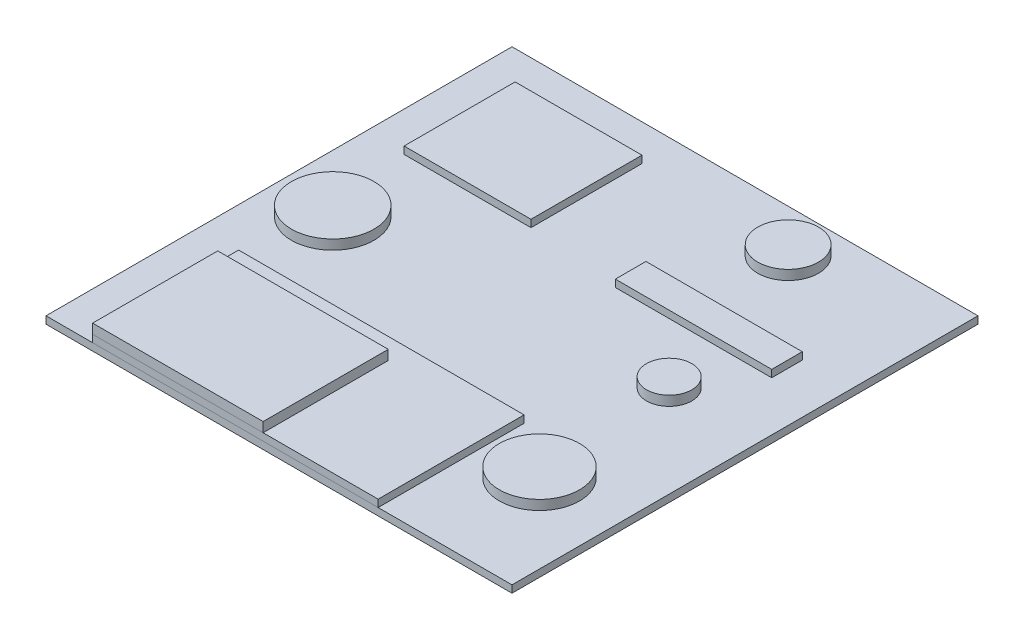
SolidWorks part; units mm, degrees
ref_plane "Front Plane" through (0, 0, 0) normal (0, 0, 1) x (1, 0, 0)
ref_plane "Top Plane" through (0, 0, 0) normal (0, 1, 0) x (1, 0, 0)
ref_plane "Right Plane" through (0, 0, 0) normal (1, 0, 0) x (0, 0, -1)
sketch "Sketch1" plane through (0, 0, 0) normal (0, 1, 0) x (1, 0, 0)
  line L1 (-609.6, -609.6) -> (609.6, -609.6)
  line L2 (-609.6, -609.6) -> (-609.6, 609.6)
  line L3 (-609.6, 609.6) -> (609.6, 609.6)
  line L4 (609.6, -609.6) -> (609.6, 609.6)
  line L5 (-609.6, -609.6) -> (609.6, 609.6) construction
  line L6 (-609.6, 609.6) -> (609.6, -609.6) construction
  point P0 (0, 0)
  dimension "D1" = 1219.2
  dimension "D2" = 1219.2
extrude "Extrude1" add sketch "Sketch1" along normal blind 19.05
sketch "Sketch2" plane through (0, 19.05, 0) normal (0, 1, 0) x (1, 0, 0)
  line L0 (-609.6, -609.6) -> (609.6, -609.6) construction
  line L1 (-506.8128, 514.9633) -> (-174.8652, 514.9633)
  line L2 (-506.8128, 514.9633) -> (-506.8128, 224.5092)
  line L3 (-506.8128, 224.5092) -> (-174.8652, 224.5092)
  line L4 (-174.8652, 514.9633) -> (-174.8652, 224.5092)
  line L5 (-506.8128, 514.9633) -> (-174.8652, 224.5092) construction
  line L6 (-506.8128, 224.5092) -> (-174.8652, 514.9633) construction
  line L7 (71.1316, 279.3398) -> (480.1384, 279.3398)
  line L8 (71.1316, 279.3398) -> (71.1316, 199.3167)
  line L9 (71.1316, 199.3167) -> (480.1384, 199.3167)
  line L10 (480.1384, 279.3398) -> (480.1384, 199.3167)
  line L11 (71.1316, 279.3398) -> (480.1384, 199.3167) construction
  line L12 (71.1316, 199.3167) -> (480.1384, 279.3398) construction
  line L13 (-487.548, -227.6784) -> (259.334, -227.6784)
  line L14 (-487.548, -227.6784) -> (-487.548, -609.6)
  line L15 (-487.548, -609.6) -> (259.334, -609.6)
  line L16 (259.334, -227.6784) -> (259.334, -609.6)
  line L17 (-487.548, -227.6784) -> (259.334, -609.6) construction
  line L18 (-487.548, -609.6) -> (259.334, -227.6784) construction
  point P0 (-340.839, 369.7362)
  point P5 (275.635, 239.3283)
  point P10 (-114.107, -418.6392)
extrude "Extrude2" add sketch "Sketch2" along normal blind 19.05 separate body
sketch "Sketch3" plane through (0, 38.1, 0) normal (0, 1, 0) x (1, 0, 0)
  line L0 (-487.548, -227.6784) -> (-487.548, -609.6) construction
  line L1 (-487.548, -282.3036) -> (-41.4934, -282.3036)
  line L2 (-487.548, -282.3036) -> (-487.548, -609.6)
  line L3 (-487.548, -609.6) -> (-41.4934, -609.6)
  line L4 (-41.4934, -282.3036) -> (-41.4934, -609.6)
  line L5 (-487.548, -609.6) -> (259.334, -609.6) construction
extrude "Extrude3" add sketch "Sketch3" along normal blind 25.4 separate body
sketch "Sketch4" plane through (0, 19.05, 0) normal (0, 1, 0) x (1, 0, 0)
  circle A0 centre (-459.3917, -9.6324) radius 107.9355
  circle A1 centre (368.9953, 42.2344) radius 59.2763
  circle A2 centre (225.2501, 497.1804) radius 79.4309
  circle A3 centre (403.0792, -331.2066) radius 104.9752
extrude "Extrude4" add sketch "Sketch4" along normal blind 25.4 separate body
